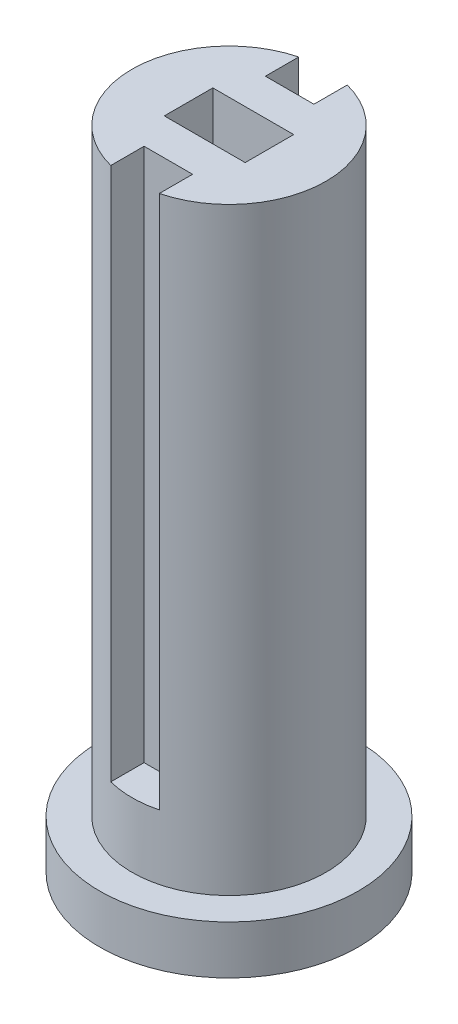
SolidWorks part; units mm, degrees
ref_plane "Plan de face" through (0, 0, 0) normal (0, 0, 1) x (1, 0, 0)
ref_plane "Plan de dessus" through (0, 0, 0) normal (0, 1, 0) x (1, 0, 0)
ref_plane "Plan de droite" through (0, 0, 0) normal (1, 0, 0) x (0, 0, -1)
sketch "Esquisse4" plane through (0, 0, 0) normal (0, 0, 1) x (1, 0, 0)
  line L0 (-10.0306, 30) -> (-10.0306, -10)
  line L1 (-4.0306, -7) -> (-4.0306, 30)
  line L2 (-10.0306, -10) -> (-2.0306, -10)
  line L3 (-2.0306, -10) -> (-2.0306, -7)
  line L4 (-2.0306, -7) -> (-4.0306, -7)
  line L5 (-4.0306, 30) -> (-10.0306, 30)
  dimension "D1" = 8
  dimension "D2" = 6
  dimension "D3" = 3
  dimension "D4" = 37
revolve "Révolution1" add sketch "Esquisse4" angle 360 about L0
sketch "Esquisse9" plane through (0, 30, 0) normal (0, 1, 0) x (1, 0, 0)
  line L0 (-10.0306, 0) -> (-10.0306, 8.8849) construction
  line L1 (-12.5306, 1.5) -> (-7.5306, 1.5)
  line L2 (-12.5306, -1.5) -> (-12.5306, -0.5)
  line L3 (-7.5306, -1.5) -> (-12.5306, -1.5)
  line L4 (-7.5306, -1.5) -> (-7.5306, -0.5)
  line L5 (-12.5306, -1.5) -> (-7.5306, 1.5) construction
  line L6 (-12.5306, 1.5) -> (-7.5306, -1.5) construction
  line L12 (-12.5306, -0.166) -> (-7.5306, 0.166) construction
  line L13 (-12.5306, 0.166) -> (-7.5306, -0.166) construction
  line L14 (-12.5306, 0.5) -> (-12.5306, 1.5)
  line L16 (-7.5306, 0.5) -> (-7.5306, 1.5)
  line L17 (-7.5306, -0.5) -> (-7.5306, 0.5)
  line L18 (-12.5306, -0.5) -> (-12.5306, 0.5)
  point P0 (-10.0306, 0)
  point P1 (-10.0306, 0)
  dimension "D1" = 3
  dimension "D2" = 5
extrude "Enlèv. mat.-Extru.4" cut sketch "Esquisse9" against normal blind 8
sketch "Esquisse11" plane through (0, 30, 0) normal (0, 1, 0) x (1, 0, 0)
  line L0 (-7.5306, 1.5) -> (-12.5306, 1.5) construction
  line L1 (-12.5306, -1.5) -> (-7.5306, -1.5) construction
  line L2 (-10.0306, 0) -> (-5.2646, 0) construction
  line L3 (-10.0306, 0) -> (-10.0306, 9.6145) construction
  line L4 (-10.0306, 3.75) -> (-11.5306, 3.75)
  line L5 (-11.5306, 3.75) -> (-11.5306, 6.1473)
  line L6 (-11.5306, 6.1473) -> (-8.5306, 6.1473)
  line L7 (-8.5306, 6.1473) -> (-8.5306, 3.75)
  line L8 (-8.5306, 3.75) -> (-10.0306, 3.75)
  line L9 (-8.5306, -3.75) -> (-10.0306, -3.75)
  line L10 (-8.5306, -6.1473) -> (-8.5306, -3.75)
  line L11 (-11.5306, -6.1473) -> (-8.5306, -6.1473)
  line L12 (-11.5306, -3.75) -> (-11.5306, -6.1473)
  line L13 (-10.0306, -3.75) -> (-11.5306, -3.75)
  circle A0 centre (-10.0306, 0) radius 6 construction
  point P0 (-10.0306, 1.5)
  point P1 (-10.0306, -1.5)
  point P4 (-10.0306, 0)
  point P22 (-10.0306, 6)
  dimension "D1" = 3.75
  dimension "D2" = 2.25
  dimension "D3" = 2.25
  dimension "D4" = 1.5
  dimension "D5" = 1.5
extrude "Enlèv. mat.-Extru.5" cut sketch "Esquisse11" against normal blind 33
